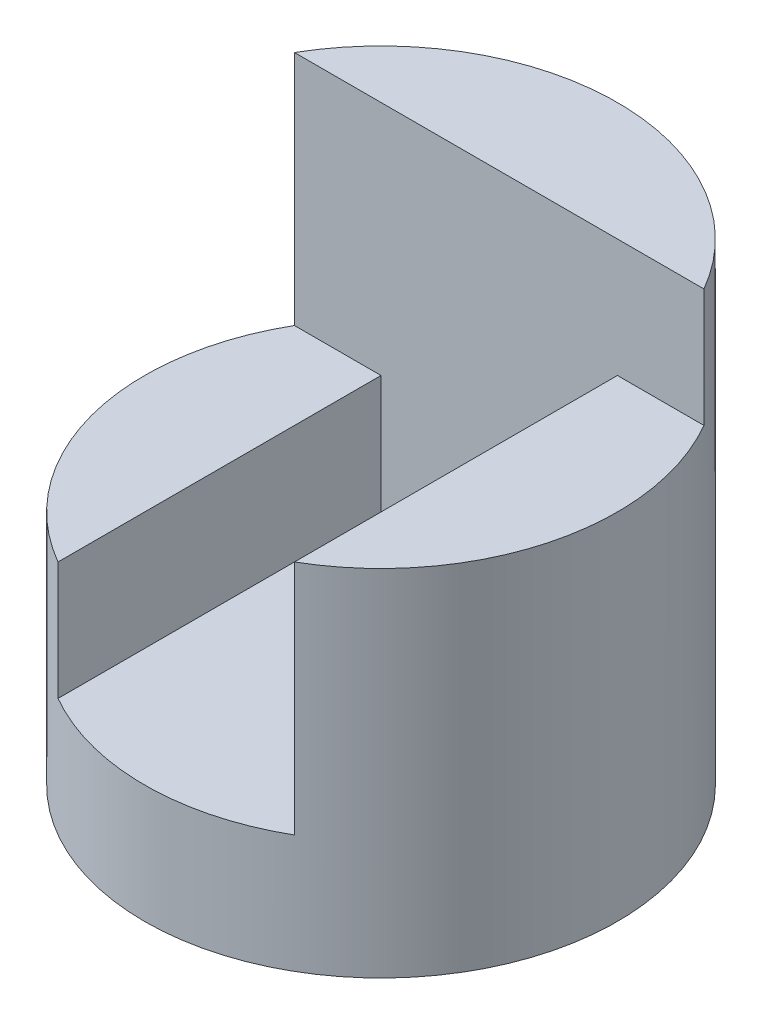
SolidWorks part; units mm, degrees
ref_plane "Front" through (0, 0, 0) normal (0, 0, 1) x (1, 0, 0)
ref_plane "Top" through (0, 0, 0) normal (0, 1, 0) x (1, 0, 0)
ref_plane "Right" through (0, 0, 0) normal (1, 0, 0) x (0, 0, -1)
sketch "Sketch1" plane through (0, 0, 0) normal (0, 1, 0) x (1, 0, 0)
  circle A0 centre (0, 0) radius 2
  dimension "D1" = 4
extrude "Boss-Extrude1" add sketch "Sketch1" along normal blind 4
sketch "Sketch2" plane through (0, 0, 0) normal (0, 0, 1) x (1, 0, 0)
  line L0 (-2, 4) -> (2, 4)
  line L1 (2, 4) -> (2, 3)
  line L2 (2, 0) -> (2, 4) construction
  line L3 (2, 3) -> (1, 3)
  line L4 (1, 3) -> (1, 1)
  line L5 (1, 1) -> (-1, 1)
  line L6 (-1, 1) -> (-1, 3)
  line L7 (-1, 3) -> (-2, 3)
  line L8 (-2, 3) -> (-2, 4)
  dimension "D1" = 1
  dimension "D2" = 1
  dimension "D3" = 1
  dimension "D4" = 1
  dimension "D5" = 2
extrude "Cut-Extrude1" cut sketch "Sketch2" against normal blind 1 and the other way blind 3
sketch "Sketch3" plane through (0, 0, 0) normal (0, 0, 1) x (1, 0, 0)
  line L0 (-2, 3) -> (-2, 0) construction
  line L1 (-1, 3) -> (-2, 3)
  line L2 (-1, 3) -> (-1, 2)
  line L3 (-1, 2) -> (-2, 2)
  line L4 (-2, 3) -> (-2, 2)
  dimension "D1" = 1
extrude "Cut-Extrude2" cut sketch "Sketch3" against normal blind 1 and the other way blind 11
